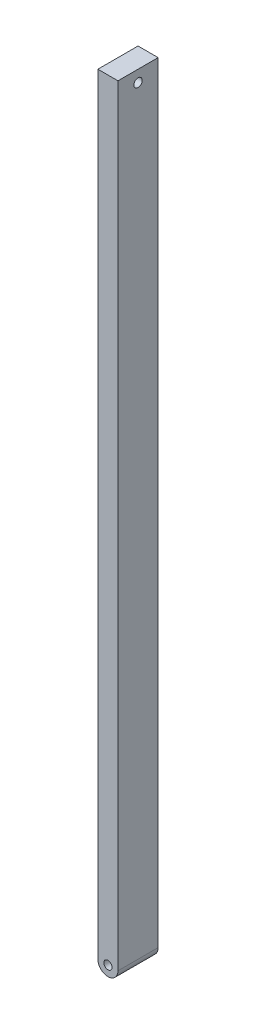
SolidWorks part; units mm, degrees
ref_plane "Front Plane" through (0, 0, 0) normal (0, 0, 1) x (1, 0, 0)
ref_plane "Top Plane" through (0, 0, 0) normal (0, 1, 0) x (1, 0, 0)
ref_plane "Right Plane" through (0, 0, 0) normal (1, 0, 0) x (0, 0, -1)
sketch "Sketch5" plane through (0, 0, 0) normal (0, 0, 1) x (1, 0, 0)
  line L0 (-1, -3.108) -> (-1, -40.898)
  line L1 (0, -3.108) -> (0, -40.898)
  line L2 (-1, -3.108) -> (-1, -2.528)
  line L3 (-1, -2.528) -> (0, -2.528)
  line L4 (0, -2.528) -> (0, -3.108)
  line L5 (-1, -3.108) -> (0, -3.108) construction
  arc A1 (-1, -40.898) -> (0, -40.898) centre (-0.5, -40.898) ccw
  circle A3 centre (-0.5, -40.898) radius 0.2039
  dimension "D1" = 1
  dimension "D2" = 37.79
  dimension "D3" = 0.58
extrude "Boss-Extrude2" add sketch "Sketch5" along normal blind 2
sketch "Sketch7" plane through (0, 0, 0) normal (1, 0, 0) x (0, 0, -1)
  line L0 (-2, -2.528) -> (-2, -3.108) construction
  line L1 (-2, -40.898) -> (-2, -2.528) construction
  line L2 (-2, -3.108) -> (0, -3.108) construction
  line L3 (0, -40.898) -> (0, -2.528) construction
  circle A0 centre (-1, -3.108) radius 0.2088
  dimension "D1" = 0.58
extrude "Cut-Extrude5" cut sketch "Sketch7" against normal through all
